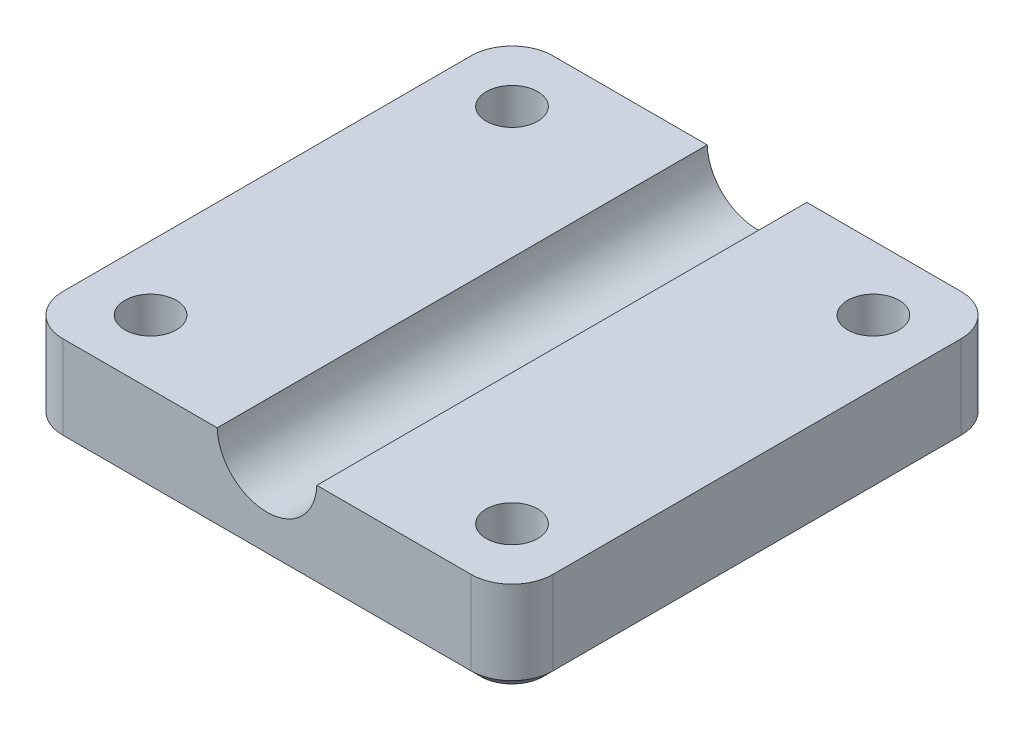
SolidWorks part; units mm, degrees
ref_plane "前视基准面" through (0, 0, 0) normal (0, 0, 1) x (1, 0, 0)
ref_plane "上视基准面" through (0, 0, 0) normal (0, 1, 0) x (1, 0, 0)
ref_plane "右视基准面" through (0, 0, 0) normal (1, 0, 0) x (0, 0, -1)
sketch "草图2" plane through (0, 0, 0) normal (0, 1, 0) x (1, 0, 0)
  line L1 (-15.24, -15.24) -> (15.24, -15.24)
  line L2 (-15.24, -15.24) -> (-15.24, 15.24)
  line L3 (-15.24, 15.24) -> (15.24, 15.24)
  line L4 (15.24, -15.24) -> (15.24, 15.24)
  line L5 (-15.24, -15.24) -> (15.24, 15.24) construction
  line L6 (-15.24, 15.24) -> (15.24, -15.24) construction
  point P0 (0, 0)
  dimension "D1" = 30.48
  dimension "D2" = 30.48
extrude "凸台-拉伸1" add sketch "草图2" along normal blind 5.8
sketch "草图3" plane through (0, 0, 15.24) normal (0, 0, 1) x (1, 0, 0)
  line L0 (0, 0) -> (0, 6) construction
  line L1 (-15.24, 5.8) -> (15.24, 5.8) construction
  circle A0 centre (0, 5.9) radius 3.1
  dimension "D2" = 6.2
  dimension "D1" = 0.1
extrude "切除-拉伸1" cut sketch "草图3" against normal up to surface (30.48 mm away) up to face at (0, 2.9, -15.24)
sketch "草图4" plane through (0, 0, 0) normal (0, -1, 0) x (1, 0, 0)
  line L0 (0, 0) -> (-15.24, 15.24) construction
  line L1 (-15.24, 15.24) -> (15.24, 15.24) construction
  line L2 (-15.24, 12.7) -> (-12.7, 15.24) construction
  line L3 (-15.24, -15.24) -> (-15.24, 15.24) construction
  line L4 (13.567, 13.567) -> (10.3883, 14.4188)
  line L5 (-13.567, 13.567) -> (-14.4188, 10.3883)
  line L6 (-14.4188, 10.3883) -> (-12.0917, 8.0612)
  line L7 (-12.0917, 8.0612) -> (-8.913, 8.913)
  line L8 (-8.913, 8.913) -> (-8.0612, 12.0917)
  line L9 (-8.0612, 12.0917) -> (-10.3883, 14.4188)
  line L10 (-10.3883, 14.4188) -> (-13.567, 13.567)
  line L11 (10.3883, 14.4188) -> (8.0612, 12.0917)
  line L12 (8.0612, 12.0917) -> (8.913, 8.913)
  line L13 (8.913, 8.913) -> (12.0917, 8.0612)
  line L14 (12.0917, 8.0612) -> (14.4188, 10.3883)
  line L15 (14.4188, 10.3883) -> (13.567, 13.567)
  line L16 (13.567, -13.567) -> (14.4188, -10.3883)
  line L17 (14.4188, -10.3883) -> (12.0917, -8.0612)
  line L18 (12.0917, -8.0612) -> (8.913, -8.913)
  line L19 (8.913, -8.913) -> (8.0612, -12.0917)
  line L20 (8.0612, -12.0917) -> (10.3883, -14.4188)
  line L21 (10.3883, -14.4188) -> (13.567, -13.567)
  line L22 (-13.567, -13.567) -> (-10.3883, -14.4188)
  line L23 (-10.3883, -14.4188) -> (-8.0612, -12.0917)
  line L24 (-8.0612, -12.0917) -> (-8.913, -8.913)
  line L25 (-8.913, -8.913) -> (-12.0917, -8.0612)
  line L26 (-12.0917, -8.0612) -> (-14.4188, -10.3883)
  line L27 (-14.4188, -10.3883) -> (-13.567, -13.567)
  circle A4 centre (-11.24, 11.24) radius 2.85 construction
  point P39 (0, 0)
  dimension "D1" = 4
  dimension "D3" = 5.7
  dimension "D4" = 2.54
  dimension "D5" = 45
  dimension "D2" = 4
extrude "切除-拉伸2" cut sketch "草图4" against normal blind 2.5
sketch "草图5" plane through (0, 2.5, 0) normal (0, -1, 0) x (-1, 0, 0)
  line L0 (13.567, -13.567) -> (8.913, -8.913) construction
  circle A0 centre (11.24, -11.24) radius 1.6
  circle A1 centre (-11.24, -11.24) radius 1.6
  circle A2 centre (-11.24, 11.24) radius 1.6
  circle A3 centre (11.24, 11.24) radius 1.6
  point P15 (0, 0)
  dimension "D1" = 3.2
  dimension "D2" = 4
extrude "切除-拉伸3" cut sketch "草图5" against normal up to surface (3.3 mm away) up to face at (9.1692, 5.8, 0)
fillet "圆角1" radius 2.54 4 edges at (-15.24, 2.9, -15.24) (-15.24, 2.9, 15.24) (15.24, 2.9, 15.24) (15.24, 2.9, -15.24)
chamfer "倒角1" distance 0.6 angle 45 8 edges at (0, 0, -15.24) (-14.4961, 0, -14.4961) (14.4961, 0, -14.4961) (-15.24, 0, 0) (15.24, 0, 0) (-14.4961, 0, 14.4961) (14.4961, 0, 14.4961) (0, 0, 15.24)
